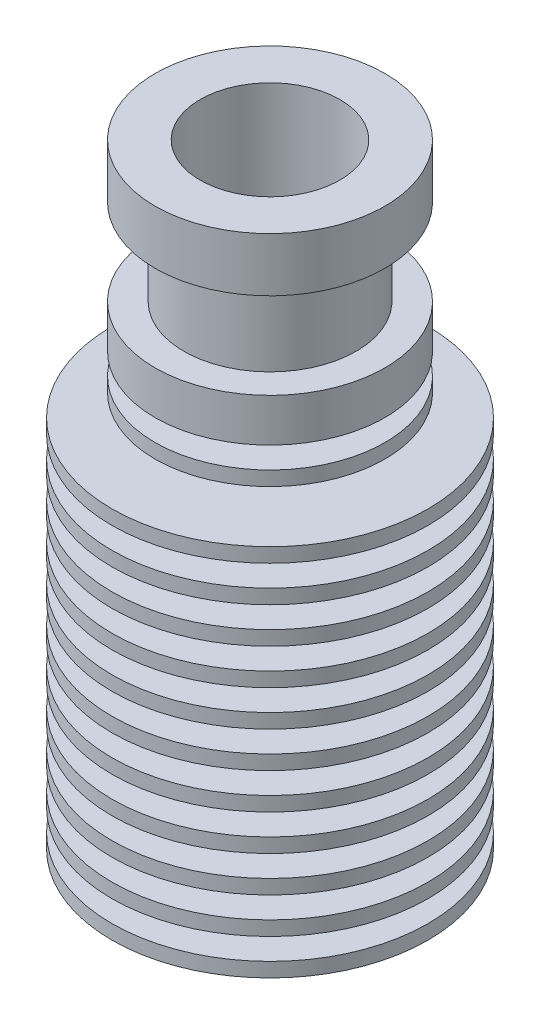
SolidWorks part; units mm, degrees
material "1060 Alloy"
ref_plane "Front Plane" through (0, 0, 0) normal (0, 0, 1) x (1, 0, 0)
ref_plane "Top Plane" through (0, 0, 0) normal (0, 1, 0) x (1, 0, 0)
ref_plane "Right Plane" through (0, 0, 0) normal (1, 0, 0) x (0, 0, -1)
sketch "Sketch1" plane through (0, 0, 0) normal (0, 0, 1) x (1, 0, 0)
  line L0 (0, -21.375) -> (0, 21.375) construction
  line L1 (3, -21.375) -> (11, -21.375)
  line L2 (11, -21.375) -> (11, -20.375)
  line L3 (11, -20.375) -> (4, -20.375)
  line L4 (4, -20.375) -> (4, -18.875)
  line L5 (4, -18.875) -> (11, -18.875)
  line L6 (11, -18.875) -> (11, -17.875)
  line L7 (11, -17.875) -> (4, -17.875)
  line L8 (4, -17.875) -> (4, -16.375)
  line L9 (4, -16.375) -> (11, -16.375)
  line L10 (11, -16.375) -> (11, -15.375)
  line L11 (11, -15.375) -> (4, -15.375)
  line L12 (4, -15.375) -> (4, -13.875)
  line L13 (4, -13.875) -> (11, -13.875)
  line L14 (11, -13.875) -> (11, -12.875)
  line L15 (11, -12.875) -> (4, -12.875)
  line L16 (4, -12.875) -> (4, -11.375)
  line L17 (4, -11.375) -> (11, -11.375)
  line L18 (11, -11.375) -> (11, -10.375)
  line L19 (11, -10.375) -> (4, -10.375)
  line L20 (4, -10.375) -> (4, -8.875)
  line L21 (4, -8.875) -> (11, -8.875)
  line L22 (11, -8.875) -> (11, -7.875)
  line L23 (11, -7.875) -> (4, -7.875)
  line L24 (4, -7.875) -> (4, -6.375)
  line L25 (4, -6.375) -> (11, -6.375)
  line L26 (11, -6.375) -> (11, -5.375)
  line L27 (11, -5.375) -> (4, -5.375)
  line L28 (4, -5.375) -> (4, -3.875)
  line L29 (4, -3.875) -> (11, -3.875)
  line L30 (11, -3.875) -> (11, -2.875)
  line L31 (11, -2.875) -> (4, -2.875)
  line L32 (4, -2.875) -> (4, -1.375)
  line L33 (4, -1.375) -> (11, -1.375)
  line L34 (11, -1.375) -> (11, -0.375)
  line L35 (11, -0.375) -> (4, -0.375)
  line L36 (4, -0.375) -> (4, 1.125)
  line L37 (4, 1.125) -> (11, 1.125)
  line L38 (11, 1.125) -> (11, 2.125)
  line L39 (11, 2.125) -> (4, 2.125)
  line L40 (4, 2.125) -> (4, 3.625)
  line L41 (4, 3.625) -> (11, 3.625)
  line L42 (11, 3.625) -> (11, 4.625)
  line L43 (8, 7.125) -> (4, 7.125)
  line L44 (4, 7.125) -> (4, 8.625)
  line L45 (4, 8.625) -> (8, 8.625)
  line L46 (8, 8.625) -> (8, 11.625)
  line L47 (8, 11.625) -> (6, 11.625)
  line L48 (6, 11.625) -> (6, 17.625)
  line L49 (6, 17.625) -> (8, 17.625)
  line L50 (8, 17.625) -> (8, 21.375)
  line L51 (3, -21.375) -> (3, -7.05)
  line L52 (3, -7.05) -> (1, -5.8953)
  line L53 (1, -5.8953) -> (1, 1.8369)
  line L54 (1, 1.8369) -> (2, 2.4142)
  line L55 (2, 2.4142) -> (2, 6.4142)
  line L56 (2, 6.4142) -> (4.8641, 11.375)
  line L57 (4.8641, 11.375) -> (4.8641, 21.375)
  line L58 (4.8641, 21.375) -> (8, 21.375)
  line L59 (11, 4.625) -> (4, 4.625)
  line L60 (4, 4.625) -> (4, 6.125)
  line L61 (4, 6.125) -> (8, 6.125)
  line L62 (8, 6.125) -> (8, 7.125)
  point P66 (7.5, 4.625)
  dimension "D2" = 3
  dimension "D3" = 22
  dimension "D4" = 1
  dimension "D5" = 1.5
  dimension "D6" = 8
  dimension "D7" = 8
  dimension "D8" = 8
  dimension "D9" = 6
  dimension "D10" = 3.75
  dimension "D11" = 16
  dimension "D12" = 26
  dimension "D13" = 3
  dimension "D14" = 12
  dimension "D15" = 2
  dimension "D16" = 4
  dimension "D17" = 42.75
  dimension "D18" = 4
  dimension "D19" = 10
  dimension "D20" = 150
  dimension "D21" = 4.8641
  dimension "D22" = 120
  dimension "D23" = 120
  dimension "D24" = 7
revolve "Revolve1" add sketch "Sketch1" angle 360 about L0
